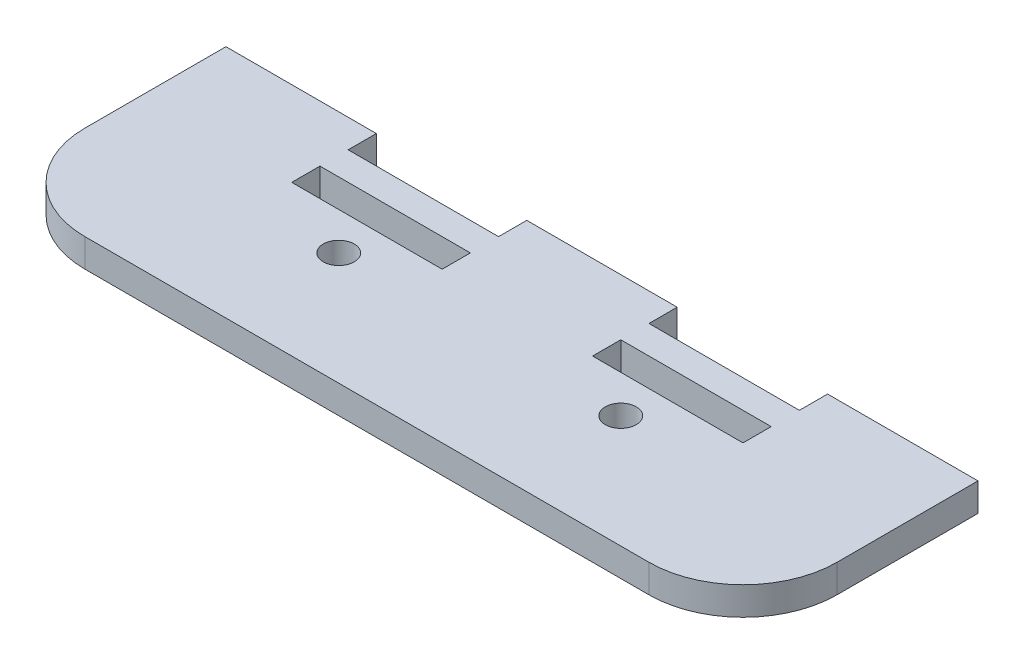
SolidWorks part; units mm, degrees
ref_plane "Ön Düzlem" through (0, 0, 0) normal (0, 0, 1) x (1, 0, 0)
ref_plane "Üst Düzlem" through (0, 0, 0) normal (0, 1, 0) x (1, 0, 0)
ref_plane "Sağ Düzlem" through (0, 0, 0) normal (1, 0, 0) x (0, 0, -1)
sketch "Sketch1" plane through (0, 0, 0) normal (0, 1, 0) x (1, 0, 0)
  line L0 (-40, 12.5) -> (-40, 9.5) construction
  line L1 (30, -12.5) -> (-30, -12.5)
  line L2 (40, -2.5) -> (40, 12.5)
  line L3 (40, 12.5) -> (24, 12.5)
  line L4 (-40, -2.5) -> (-40, 12.5)
  line L5 (40, -12.5) -> (0, 0) construction
  line L6 (40, 12.5) -> (-40, -12.5) construction
  line L7 (-40, 9.5) -> (-40, 5.8835) construction
  line L8 (-40, 5.8835) -> (-40, 3.2973) construction
  line L9 (-24, 6.5) -> (-24, 3.5)
  line L10 (-24, 3.5) -> (-8, 3.5)
  line L11 (-40, 9.5) -> (40, 9.5) construction
  line L12 (-40, 9.5) -> (-24, 9.5) construction
  line L13 (-24, 9.5) -> (-24, 12.5)
  line L14 (-24, 9.5) -> (-8, 9.5)
  line L15 (-8, 9.5) -> (-8, 12.5)
  line L16 (40, 9.5) -> (24, 9.5) construction
  line L17 (24, 9.5) -> (24, 12.5)
  line L18 (24, 9.5) -> (8, 9.5)
  line L19 (8, 9.5) -> (8, 12.5)
  line L20 (-24, 12.5) -> (-40, 12.5)
  line L21 (8, 12.5) -> (-8, 12.5)
  line L30 (-8, 3.5) -> (-8, 6.5)
  line L31 (-24, 6.5) -> (-8, 6.5)
  line L32 (8, 6.5) -> (8, 3.5)
  line L33 (8, 6.5) -> (24, 6.5)
  line L34 (8, 3.5) -> (24, 3.5)
  line L35 (-18.8274, 5.8835) -> (-40, 12.5) construction
  line L36 (24, 3.5) -> (24, 6.5)
  circle A0 centre (-15, -0.5) radius 1.65
  circle A1 centre (15, -0.5) radius 1.65
  arc A2 (-40, -2.5) -> (-30, -12.5) centre (-30, -2.5) ccw
  arc A3 (40, -2.5) -> (30, -12.5) centre (30, -2.5) cw
  point P0 (0, 0)
  dimension "D3" = 10
  dimension "D4" = 10
  dimension "D1" = 25
  dimension "D2" = 80
extrude "Boss-Extrude1" add sketch "Sketch1" along normal blind 3
